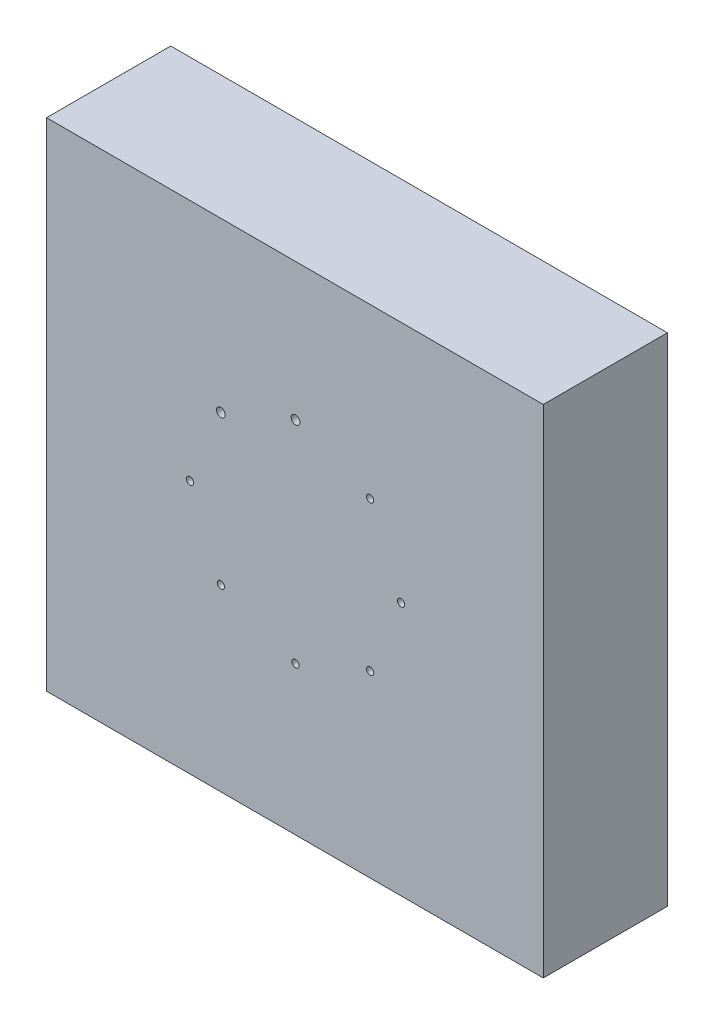
SolidWorks part; units mm, degrees
ref_plane "前视基准面" through (0, 0, 0) normal (0, 0, 1) x (1, 0, 0)
ref_plane "上视基准面" through (0, 0, 0) normal (0, 1, 0) x (1, 0, 0)
ref_plane "右视基准面" through (0, 0, 0) normal (1, 0, 0) x (0, 0, -1)
other "Configuration Table"
sketch "草图1" plane through (0, 0, 0) normal (0, 0, 1) x (1, 0, 0)
  line L1 (-100, -100) -> (100, -100)
  line L2 (-100, -100) -> (-100, 100)
  line L3 (-100, 100) -> (100, 100)
  line L4 (100, -100) -> (100, 100)
  line L5 (-100, -100) -> (100, 100) construction
  line L6 (-100, 100) -> (100, -100) construction
  point P0 (0, 0)
  dimension "D1" = 200
  dimension "D2" = 200
extrude "凸台-拉伸1" add sketch "草图1" along normal blind 50
sketch "草图6" plane through (0, 0, 0) normal (0, 0, -1) x (-1, 0, 0)
  circle A0 centre (42.25, 2.25) radius 1.4496
  circle A1 centre (29.802, 32.302) radius 1.75
  circle A2 centre (-0.2505, 44.75) radius 1.7505
  circle A3 centre (-30.302, 32.302) radius 1.4394
  circle A4 centre (-42.7503, 2.2497) radius 1.45
  circle A5 centre (-30.3021, -27.8022) radius 1.45
  circle A6 centre (-0.25, -40.25) radius 1.45
  circle A7 centre (29.802, -27.802) radius 1.4501
sketch "草图7" plane through (0, 0, 50) normal (0, 0, 1) x (1, 0, 0)
  line L4 (100, -100) -> (100, 100)
  line L5 (100, 100) -> (-100, 100)
  line L6 (-100, 100) -> (-100, -100)
  line L7 (-100, -100) -> (100, -100)
  line L8 (100, -100) -> (100, 100)
  line L9 (100, 100) -> (-100, 100)
  line L10 (-100, 100) -> (-100, -100)
  line L11 (-100, -100) -> (100, -100)
  circle A0 centre (-29.802, 32.302) radius 1.75 construction
  circle A1 centre (-42.25, 2.25) radius 1.4496 construction
  circle A2 centre (-29.802, -27.802) radius 1.4501 construction
  circle A3 centre (0.25, -40.25) radius 1.45 construction
  circle A4 centre (30.3021, -27.8022) radius 1.45 construction
  circle A5 centre (42.7503, 2.2497) radius 1.45 construction
  circle A6 centre (0.2505, 44.75) radius 1.7505 construction
  circle A7 centre (30.302, 32.302) radius 1.4394 construction
  circle A8 centre (-29.802, 32.302) radius 1.75
  circle A9 centre (-42.25, 2.25) radius 1.4496
  circle A10 centre (-29.802, -27.802) radius 1.4501
  circle A11 centre (0.25, -40.25) radius 1.45
  circle A12 centre (30.3021, -27.8022) radius 1.45
  circle A13 centre (42.7503, 2.2497) radius 1.45
  circle A14 centre (0.2505, 44.75) radius 1.7505
  circle A15 centre (30.302, 32.302) radius 1.4394
  dimension "D1" = 0
extrude "切除-拉伸2" cut sketch "草图7" against normal blind 5 contours A11 | A10 | A9 | A8 | A13 | A12 | A15 | A14
